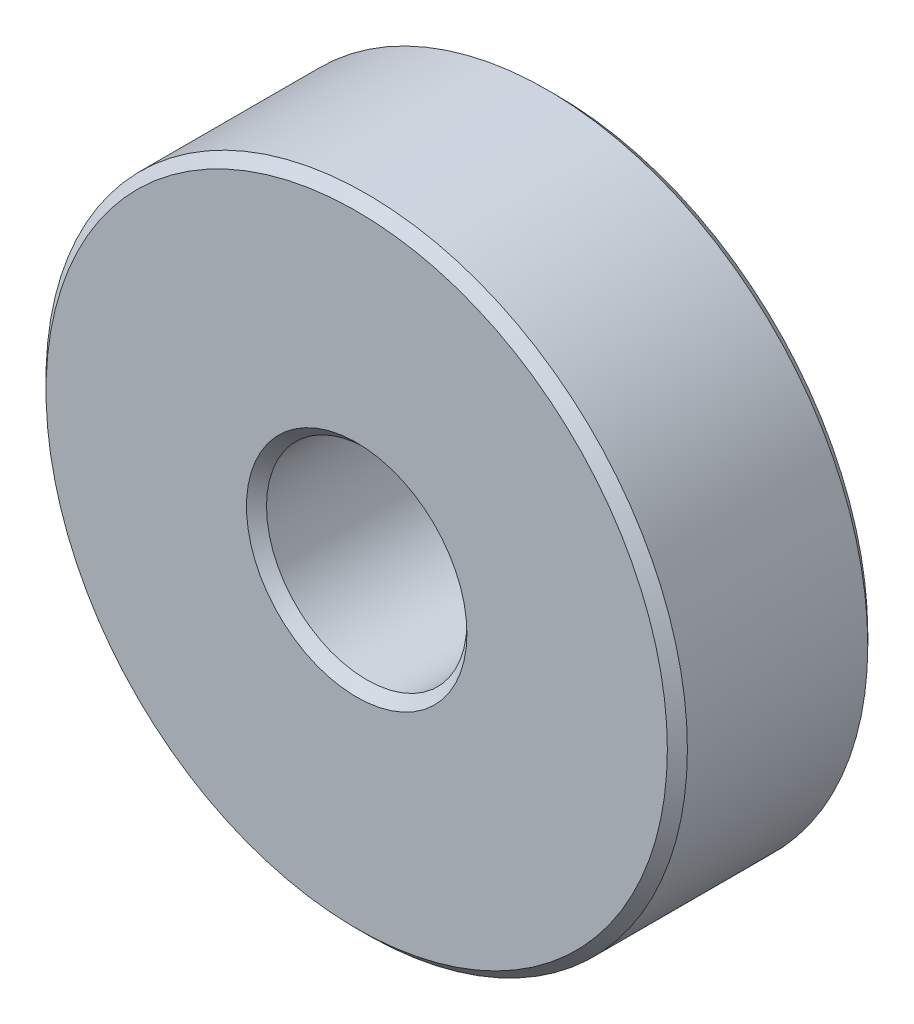
SolidWorks part; units mm, degrees
ref_plane "Front Plane" through (0, 0, 0) normal (0, 0, 1) x (1, 0, 0)
ref_plane "Top Plane" through (0, 0, 0) normal (0, 1, 0) x (1, 0, 0)
ref_plane "Right Plane" through (0, 0, 0) normal (1, 0, 0) x (0, 0, -1)
sketch "Sketch1" plane through (0, 0, 0) normal (0, 0, 1) x (1, 0, 0)
  circle A0 centre (0, 0) radius 8
  circle A1 centre (0, 0) radius 2.5
  dimension "D1" = 5
  dimension "D2" = 16
extrude "Boss-Extrude1" add sketch "Sketch1" along normal mid plane 5
chamfer "Chamfer1" distance 0.25 angle 45 4 edges at (2.5, 0, -2.5) (2.5, 0, 2.5) (8, 0, -2.5) (8, 0, 2.5)
